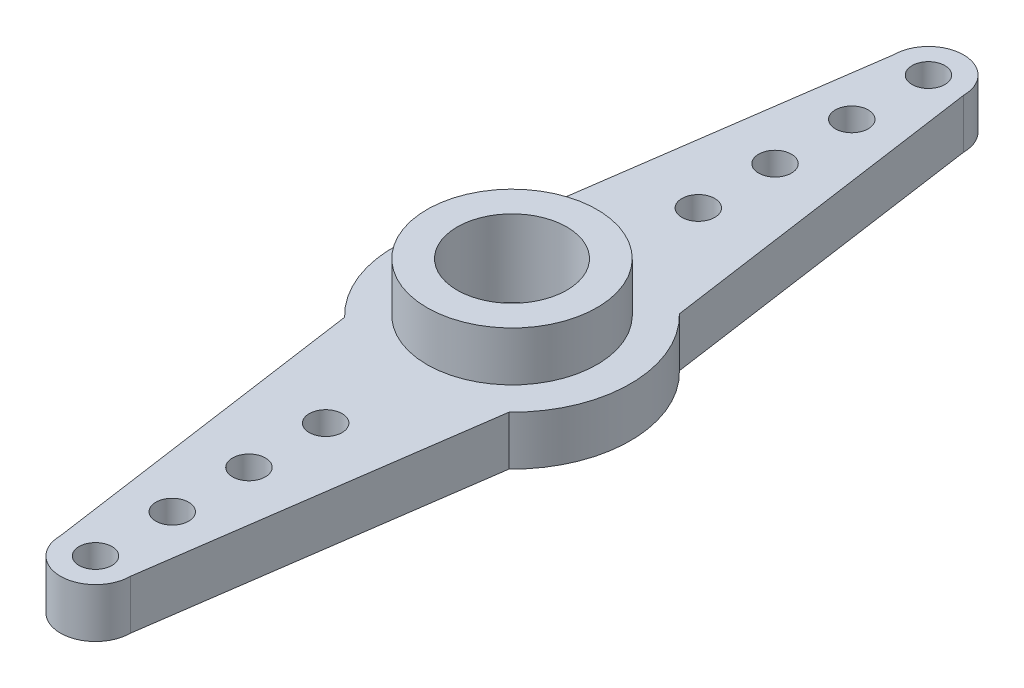
SolidWorks part; units mm, degrees
ref_plane "Front Plane" through (0, 0, 0) normal (0, 0, 1) x (1, 0, 0)
ref_plane "Top Plane" through (0, 0, 0) normal (0, 1, 0) x (1, 0, 0)
ref_plane "Right Plane" through (0, 0, 0) normal (1, 0, 0) x (0, 0, -1)
sketch "Sketch1" plane through (0, 0, 0) normal (0, 1, 0) x (1, 0, 0)
  line L0 (0, 0) -> (0, 2.5) construction
  line L1 (0, 0) -> (0, -19) construction
  line L2 (-1.6, 19) -> (-3.75, 3.8856)
  line L3 (1.6, 19) -> (3.75, 3.8856)
  line L4 (0, 0) -> (0, 19) construction
  line L5 (-3.75, 3.8856) -> (3.75, 3.8856) construction
  line L6 (1.6, -19) -> (3.75, -3.8856)
  line L7 (3.75, -3.8856) -> (-3.75, -3.8856) construction
  line L8 (-3.75, -3.8856) -> (-1.6, -19)
  circle A0 centre (0, 0) radius 2.5
  arc A1 (-3.75, 3.8856) -> (-3.75, -3.8856) centre (0, 0) ccw
  arc A2 (-1.6, -19) -> (1.6, -19) centre (0, -19) ccw
  arc A3 (1.6, 19) -> (-1.6, 19) centre (0, 19) ccw
  arc A4 (3.75, -3.8856) -> (3.75, 3.8856) centre (0, 0) ccw
  circle A5 centre (0, -19) radius 0.75
  circle A6 centre (0, 19) radius 0.75
  circle A7 centre (0, 15.5) radius 0.75
  circle A8 centre (0, 12) radius 0.75
  circle A9 centre (0, 8.5) radius 0.75
  circle A10 centre (0, -15.5) radius 0.75
  circle A11 centre (0, -12) radius 0.75
  circle A12 centre (0, -8.5) radius 0.75
  dimension "D1" = 5
  dimension "D2" = 10.8
  dimension "D4" = 3.2
  dimension "D6" = 1.5
  dimension "D7" = 3.5
  dimension "D8" = 3.5
  dimension "D9" = 3.5
  dimension "D11" = 3.5
  dimension "D12" = 3.5
  dimension "D13" = 3.5
  dimension "D3" = 19
  dimension "D5" = 7.5
extrude "Boss-Extrude1" add sketch "Sketch1" along normal blind 2.25
sketch "Sketch2" plane through (0, 2.25, 0) normal (0, 1, 0) x (1, 0, 0)
  circle A0 centre (0, 0) radius 2.5
  circle A1 centre (0, 0) radius 3.8795
extrude "Boss-Extrude2" add sketch "Sketch2" along normal blind 2.25
sketch "Sketch3" plane through (0, 0, 0) normal (0, -1, 0) x (1, 0, 0)
  circle A0 centre (0, 0) radius 2.0085
  circle A1 centre (0, 0) radius 2.5
extrude "Boss-Extrude3" add sketch "Sketch3" against normal blind 1
sketch "Sketch4" plane through (0, 0, 0) normal (0, -1, 0) x (1, 0, 0)
  circle A0 centre (0, 0) radius 3
  circle A1 centre (0, 0) radius 3.8
  dimension "D1" = 0.8
  dimension "D2" = 6
extrude "Cut-Extrude1" cut sketch "Sketch4" against normal blind 0.5
